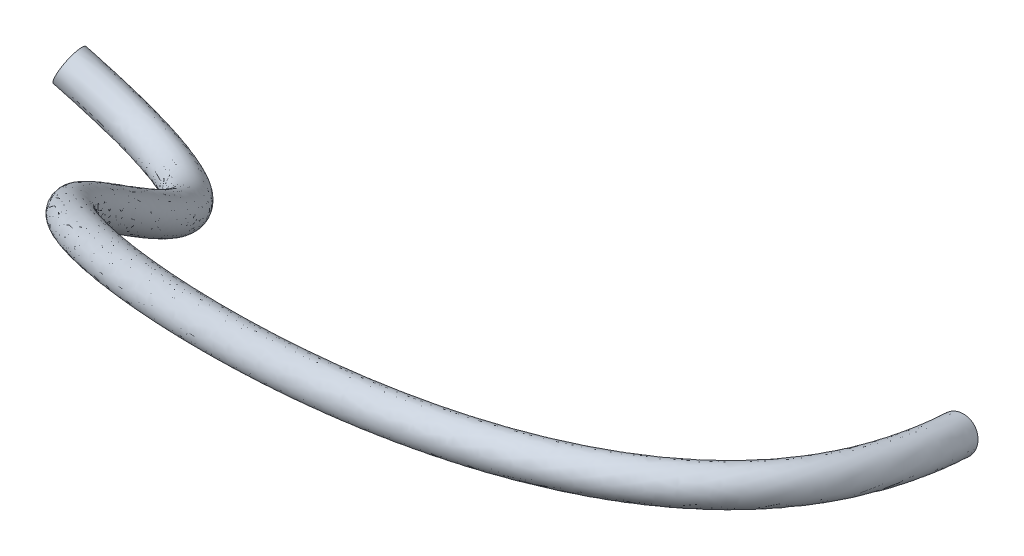
SolidWorks part; units mm, degrees
ref_plane "前视基准面" through (0, 0, 0) normal (0, 0, 1) x (1, 0, 0)
ref_plane "上视基准面" through (0, 0, 0) normal (0, 1, 0) x (1, 0, 0)
ref_plane "右视基准面" through (0, 0, 0) normal (1, 0, 0) x (0, 0, -1)
sketch3d "3D草图1"
  circle A0 centre (-201.2529, -86.6951, -61.5767) radius 4 construction
  circle A1 centre (-213.5913, -82.6019, -61.4113) radius 8.05 construction
  spline S0 degree 3 poles (0, 0, 0) (14.1298, 17.815, 76.5222) (-174.3316, -6.3877, 39.7808) (-176.4811, -99.4439, -67.0265) (-213.5913, -82.6019, -61.4113) knots 0 0 0 0 0.644857 1 1 1 1
  point P2 (0, 0, 0)
  point P4 (-17.7736, 21.3686, 19.556)
  point P6 (-20.6312, 6.4063, 26.0869)
  point P8 (-2.5434, 5.9353, 28.8897)
  point P13 (-205.0491, -85.4357, -61.5258)
  point P16 (-205.9514, -85.1364, -61.5137)
sweep "扫描1" add path "3D草图1" circular profile diameter 6 parameters "D3"=6
